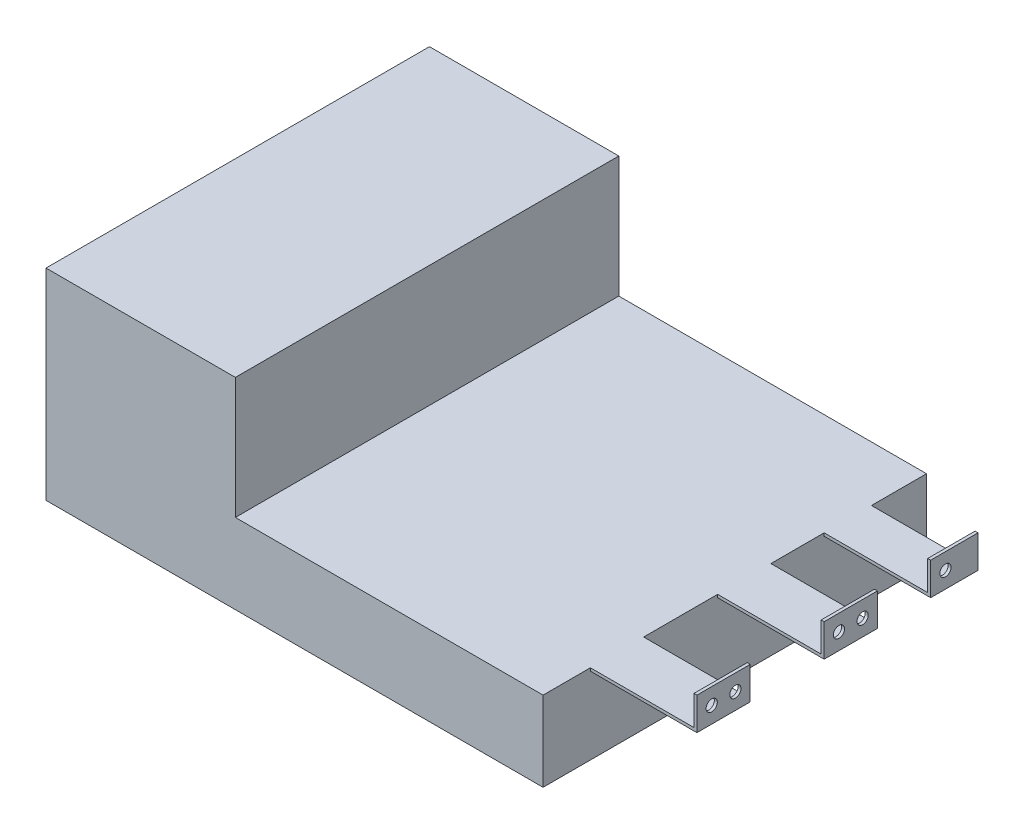
SolidWorks part; units mm, degrees
ref_plane "Front Plane" through (0, 0, 0) normal (0, 0, 1) x (1, 0, 0)
ref_plane "Top Plane" through (0, 0, 0) normal (0, 1, 0) x (1, 0, 0)
ref_plane "Right Plane" through (0, 0, 0) normal (1, 0, 0) x (0, 0, -1)
sketch "Sketch1" plane through (0, 0, 0) normal (0, 1, 0) x (1, 0, 0)
  line L0 (101.6, 205.74) -> (101.6, 0)
  line L1 (0, 0) -> (266.7, 0)
  line L2 (0, 0) -> (0, 205.74)
  line L3 (0, 205.74) -> (266.7, 205.74)
  line L4 (266.7, 0) -> (266.7, 205.74)
  dimension "D1" = 266.7
  dimension "D2" = 205.74
  dimension "D3" = 101.6
extrude "Battery Side" add sketch "Sketch1" along normal blind 107.95 contours L3 L2 L1 L0
sketch "Sketch6" plane through (0, 0, 0) normal (-1, 0, 0) x (0, 0, 1)
  line L0 (0, 0) -> (-205.74, 0) construction
  line L1 (-181.9275, 39.6875) -> (-121.6025, 39.6875)
  line L2 (-181.9275, 39.6875) -> (-181.9275, 38.1)
  line L3 (-181.9275, 38.1) -> (-121.6025, 38.1)
  line L4 (-121.6025, 39.6875) -> (-121.6025, 38.1)
  line L5 (-89.8525, 39.6875) -> (-37.465, 39.6875)
  line L6 (-89.8525, 39.6875) -> (-89.8525, 38.1)
  line L7 (-89.8525, 38.1) -> (-37.465, 38.1)
  line L8 (-37.465, 39.6875) -> (-37.465, 38.1)
  line L9 (-205.74, 107.95) -> (-205.74, 0) construction
  dimension "D1" = 1.5875
  dimension "D2" = 39.6875
  dimension "D3" = 23.8125
  dimension "D4" = 60.325
  dimension "D5" = 31.75
  dimension "D6" = 52.3875
extrude "Battery Tab Bases" add sketch "Sketch6" along normal blind 9.525
sketch "Sketch7" plane through (0, 39.6875, 0) normal (0, 1, 0) x (1, 0, 0)
  line L0 (-9.525, 121.6025) -> (0, 121.6025) construction
  line L1 (-9.525, 181.9275) -> (-7.9375, 181.9275)
  line L2 (-9.525, 181.9275) -> (-9.525, 121.6025)
  line L3 (-9.525, 121.6025) -> (-7.9375, 121.6025)
  line L4 (-7.9375, 181.9275) -> (-7.9375, 121.6025)
  line L5 (-9.525, 37.465) -> (0, 37.465) construction
  line L6 (-9.525, 89.8525) -> (-7.9375, 89.8525)
  line L7 (-9.525, 89.8525) -> (-9.525, 37.465)
  line L8 (-9.525, 37.465) -> (-7.9375, 37.465)
  line L9 (-7.9375, 89.8525) -> (-7.9375, 37.465)
  dimension "D1" = 1.5875
extrude "Battery Tabs" add sketch "Sketch7" along normal blind 25.4
sketch "Sketch8" plane through (-9.525, 0, 0) normal (-1, 0, 0) x (0, 0, 1)
  line L0 (-172.4951, 50.0063) -> (-55.2638, 50.0063) construction
  line L1 (0, 0) -> (-205.74, 0) construction
  circle A0 centre (-172.4951, 50.0063) radius 3
  circle A1 centre (-55.2638, 50.0063) radius 3
  dimension "D1" = 6
  dimension "D2" = 6
  dimension "D3" = 50.0063
extrude "Battery Tab Holes" cut sketch "Sketch8" against normal up to next
sketch "Sketch2" plane through (0, 0, 0) normal (0, 1, 0) x (1, 0, 0)
  line L0 (0, 0) -> (266.7, 0) construction
  line L1 (0, 205.74) -> (266.7, 205.74) construction
  line L2 (266.7, 0) -> (266.7, 205.74) construction
  line L3 (101.6, 205.74) -> (101.6, 0) construction
  line L4 (0, 0) -> (266.7, 0)
  line L5 (0, 205.74) -> (266.7, 205.74)
  line L6 (266.7, 0) -> (266.7, 205.74)
  line L7 (101.6, 205.74) -> (101.6, 0)
extrude "Motor Side" add sketch "Sketch2" along normal blind 42.8625 contours L5 L7 L4 L6
sketch "Sketch3" plane through (266.7, 0, 0) normal (1, 0, 0) x (0, 0, -1)
  line L0 (0, 42.8625) -> (205.74, 42.8625) construction
  line L1 (25.4, 42.8625) -> (53.975, 42.8625)
  line L2 (25.4, 42.8625) -> (25.4, 41.275)
  line L3 (25.4, 41.275) -> (53.975, 41.275)
  line L4 (53.975, 42.8625) -> (53.975, 41.275)
  line L5 (0, 42.8625) -> (0, 0) construction
  line L6 (93.6625, 42.8625) -> (122.2375, 42.8625)
  line L7 (93.6625, 42.8625) -> (93.6625, 41.275)
  line L8 (93.6625, 41.275) -> (122.2375, 41.275)
  line L9 (122.2375, 42.8625) -> (122.2375, 41.275)
  line L10 (150.8125, 42.8625) -> (176.2125, 42.8625)
  line L11 (150.8125, 42.8625) -> (150.8125, 41.275)
  line L12 (150.8125, 41.275) -> (176.2125, 41.275)
  line L13 (176.2125, 42.8625) -> (176.2125, 41.275)
  dimension "D1" = 1.5875
  dimension "D2" = 25.4
  dimension "D3" = 28.575
  dimension "D4" = 39.6875
  dimension "D5" = 28.575
  dimension "D6" = 28.575
  dimension "D7" = 25.4
extrude "Motor Tab Bases" add sketch "Sketch3" along normal blind 57.15
sketch "Sketch4" plane through (0, 42.8625, 0) normal (0, 1, 0) x (1, 0, 0)
  line L0 (323.85, 53.975) -> (266.7, 53.975) construction
  line L1 (323.85, 25.4) -> (322.2625, 25.4)
  line L2 (323.85, 25.4) -> (323.85, 53.975)
  line L3 (323.85, 53.975) -> (322.2625, 53.975)
  line L4 (322.2625, 25.4) -> (322.2625, 53.975)
  line L5 (323.85, 122.2375) -> (266.7, 122.2375) construction
  line L6 (323.85, 93.6625) -> (322.2625, 93.6625)
  line L7 (323.85, 93.6625) -> (323.85, 122.2375)
  line L8 (323.85, 122.2375) -> (322.2625, 122.2375)
  line L9 (322.2625, 93.6625) -> (322.2625, 122.2375)
  line L10 (323.85, 176.2125) -> (266.7, 176.2125) construction
  line L11 (323.85, 150.8125) -> (322.2625, 150.8125)
  line L12 (323.85, 150.8125) -> (323.85, 176.2125)
  line L13 (323.85, 176.2125) -> (322.2625, 176.2125)
  line L14 (322.2625, 150.8125) -> (322.2625, 176.2125)
  dimension "D1" = 1.5875
extrude "Motor Tabs" add sketch "Sketch4" along normal blind 15.875
sketch "Sketch5" plane through (323.85, 0, 0) normal (1, 0, 0) x (0, 0, -1)
  line L0 (33.3375, 50.0063) -> (46.0375, 50.0063) construction
  line L1 (101.6, 50.0062) -> (114.3, 50.0062) construction
  line L2 (25.4, 58.7375) -> (53.975, 41.275) construction
  line L3 (93.6625, 58.7375) -> (122.2375, 41.275) construction
  line L4 (114.3, 50.0062) -> (158.75, 50.0062) construction
  circle A0 centre (33.3375, 50.0063) radius 3
  circle A1 centre (46.0375, 50.0063) radius 3
  circle A2 centre (101.6, 50.0062) radius 3
  circle A3 centre (114.3, 50.0062) radius 3
  circle A4 centre (158.75, 50.0062) radius 3
  point P18 (39.6875, 50.0063)
  point P19 (107.95, 50.0062)
  dimension "D1" = 6
  dimension "D2" = 6
  dimension "D3" = 6
  dimension "D4" = 6
  dimension "D5" = 6
  dimension "D6" = 12.7
  dimension "D7" = 12.7
  dimension "D8" = 68.2625
  dimension "D9" = 57.15
extrude "Motor Tab Holes" cut sketch "Sketch5" against normal up to next
